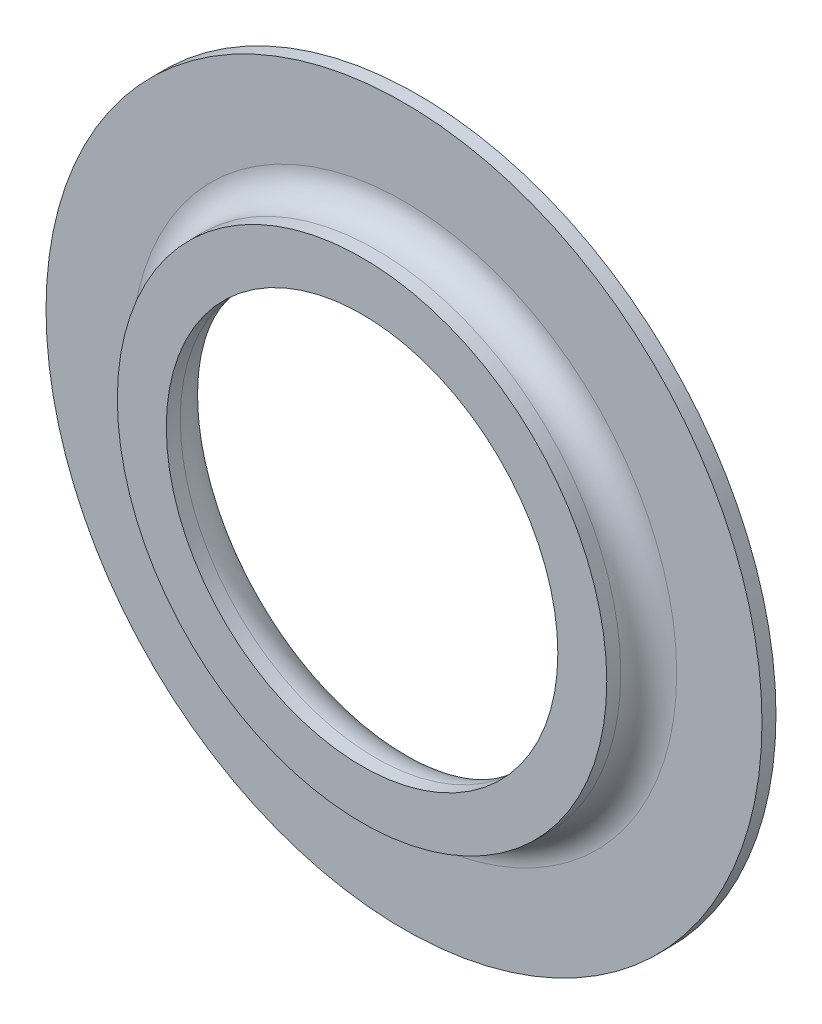
SolidWorks part; units mm, degrees
ref_plane "前视基准面" through (0, 0, 0) normal (0, 0, 1) x (1, 0, 0)
ref_plane "上视基准面" through (0, 0, 0) normal (0, 1, 0) x (1, 0, 0)
ref_plane "右视基准面" through (0, 0, 0) normal (1, 0, 0) x (0, 0, -1)
sketch "草图1" plane through (0, 0, 0) normal (0, 0, 1) x (1, 0, 0)
  circle A0 centre (0, 0) radius 25.6
  circle A1 centre (0, 0) radius 14
  dimension "D1" = 51.2
  dimension "D2" = 28
extrude "凸台-拉伸1" add sketch "草图1" along normal blind 1
sketch "草图2" plane through (0, 0, 1) normal (0, 0, 1) x (1, 0, 0)
  circle A1 centre (0, 0) radius 17.5
  circle A3 centre (0, 0) radius 14 construction
  circle A4 centre (0, 0) radius 14
  dimension "D2" = 35
extrude "凸台-拉伸2" add sketch "草图2" along normal blind 3
fillet "圆角2" radius 2 1 edges at (17.5, 0, 1)
fillet "圆角3" radius 3 1 edges at (14, 0, 0)
